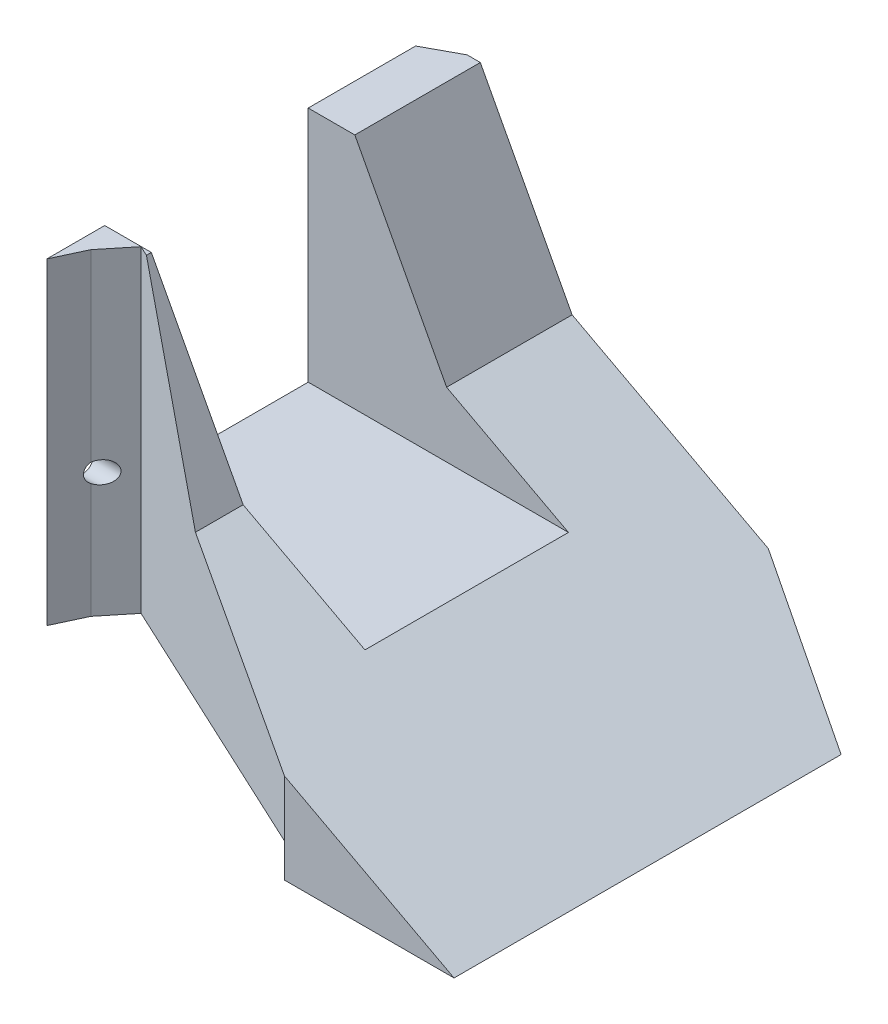
SolidWorks part; units mm, degrees
ref_plane "Alzado" through (0, 0, 0) normal (0, 0, 1) x (1, 0, 0)
ref_plane "Planta" through (0, 0, 0) normal (0, 1, 0) x (1, 0, 0)
ref_plane "Vista lateral" through (0, 0, 0) normal (1, 0, 0) x (0, 0, -1)
sketch "Croquis1" plane through (0, 0, 0) normal (1, 0, 0) x (0, 0, -1)
  line L1 (0, 0) -> (67, 0)
  line L2 (0, 0) -> (0, 51.82)
  line L3 (0, 51.82) -> (67, 51.82)
  line L4 (67, 0) -> (67, 51.82)
  dimension "D1" = 51.82
  dimension "D2" = 67
extrude "Saliente-Extruir1" add sketch "Croquis1" along normal blind 70
sketch "Croquis3" plane through (0, 0, 0) normal (0, 0, 1) x (1, 0, 0)
  line L0 (70, 0) -> (20.4044, 26.3705)
  line L1 (70, 0) -> (0, 0) construction
  line L2 (20.4044, 26.3705) -> (6.8726, 51.82)
  line L3 (70, 51.82) -> (0, 51.82) construction
  line L4 (6.8726, 51.82) -> (70, 51.82)
  line L5 (70, 51.82) -> (70, 0)
  dimension "D1" = 28
  dimension "D2" = 146
extrude "Cortar-Extruir1" cut sketch "Croquis3" against normal up to next
sketch "Croquis4" plane through (0, 51.82, 0) normal (0, 1, 0) x (1, 0, 0)
  line L0 (0, 0) -> (0, 18.5) construction
  line L1 (0, 67) -> (0, 48.5) construction
  line L2 (0, 67) -> (0, 0) construction
  line L4 (0, 18.5) -> (60, 18.5)
  line L5 (0, 18.5) -> (0, 48.5)
  line L6 (0, 48.5) -> (60, 48.5)
  line L7 (60, 18.5) -> (60, 48.5)
  dimension "D1" = 60
extrude "Cortar-Extruir2" cut sketch "Croquis4" against normal blind 35
sketch "Croquis5" plane through (0, 0, 0) normal (0, 0, 1) x (1, 0, 0)
  line L1 (0, 0) -> (45, 0)
  line L2 (0, 0) -> (0, 5)
  line L3 (0, 5) -> (45, 5)
  line L4 (45, 0) -> (45, 5)
  dimension "D1" = 5
  dimension "D2" = 45
extrude "Cortar-Extruir3" cut sketch "Croquis5" against normal up to next
sketch "Croquis6" plane through (0, 51.82, 0) normal (0, 1, 0) x (1, 0, 0)
  line L0 (4.9229, 67) -> (0, 64.3347)
  line L1 (0, 67) -> (4.9229, 67)
  line L2 (6.8726, 67) -> (0, 67) construction
  line L3 (0, 67) -> (0, 64.3347)
  line L4 (0, 67) -> (0, 48.5) construction
extrude "Cortar-Extruir4" cut sketch "Croquis6" against normal up to next
sketch "Croquis8" plane through (0, 51.82, 0) normal (0, 1, 0) x (1, 0, 0)
  line L0 (45, 0) -> (5.3768, 18.4766)
  line L1 (5.3768, 18.4766) -> (2.0593, 14.3925)
  line L2 (2.0593, 14.3925) -> (0, 9.9763)
  line L3 (0, 18.5) -> (0, 0) construction
  line L4 (-4.6588, -0.0146) -> (2.0593, 14.3925) construction
  line L5 (0, 9.9763) -> (0, -0.0622)
  line L7 (45, 0) -> (20.4044, 0)
  line L8 (20.4044, 0) -> (6.8726, 0)
  line L9 (6.8726, 0) -> (0, -0.0622)
extrude "Cortar-Extruir5" cut sketch "Croquis8" against normal up to next
sketch "Croquis9" plane through (0, 0, 0) normal (-1, 0, 0) x (0, 0, 1)
  circle A0 centre (-15.25, 23.32) radius 1.6
  circle A1 centre (-52.25, 23.32) radius 1.5221
extrude "Cortar-Extruir6" cut sketch "Croquis9" against normal blind 6
sketch "Croquis11" plane through (0, 5, 0) normal (0, -1, 0) x (1, 0, 0)
  line L0 (45, -67) -> (35, -67) construction
  line L1 (4.9229, -67) -> (45, -67) construction
  line L2 (35, -67) -> (35, -58) construction
  line L3 (0, -58) -> (10, -58) construction
  line L4 (0, -64.3347) -> (0, -9.9763) construction
  line L5 (10, -58) -> (10, -38) construction
  line L6 (10, -38) -> (35, -38) construction
  line L7 (35, -38) -> (35, -13) construction
  line L8 (10, -24.168) -> (10, -19.3014) construction
  line L9 (2.0593, -14.3925) -> (5.3768, -18.4766) construction
  circle A0 centre (35, -58) radius 1.75
  circle A1 centre (10, -58) radius 1.75
  circle A2 centre (10, -38) radius 1.75
  circle A3 centre (35, -38) radius 1.75
  circle A4 centre (10, -19.3014) radius 1.75
  circle A5 centre (35, -13) radius 1.75
  dimension "D1" = 3.5
  dimension "D2" = 3.5
  dimension "D3" = 3.5
  dimension "D4" = 3.5
  dimension "D5" = 3.5
  dimension "D6" = 3.5
extrude "Cortar-Extruir7" cut sketch "Croquis11" against normal blind 6
sketch "Croquis13" plane through (15.4282, 29.0163, 0) normal (0.4695, 0.8829, 0) x (0.8829, -0.4695, 0)
  line L0 (6.8258, 80.3974) -> (82.3656, 48.3327) construction
  line L1 (34.4679, 68.664) -> (75.1831, 51.3814)
  line L2 (75.1831, 51.3814) -> (75.1831, 68.664)
  line L3 (75.1831, 68.664) -> (34.4679, 68.664)
  line L4 (61.8063, 33.5) -> (25.9788, 33.5) construction
  line L5 (25.9788, 48.5) -> (34.4679, 68.664) construction
  line L6 (61.8063, 0) -> (61.8063, 67) construction
  line L7 (25.9788, 48.5) -> (25.9788, 18.5) construction
  dimension "D1" = 67
  dimension "D2" = 40.7153
  dimension "D3" = 20.164
extrude "Cortar-Extruir8" cut sketch "Croquis13" against normal up to next
